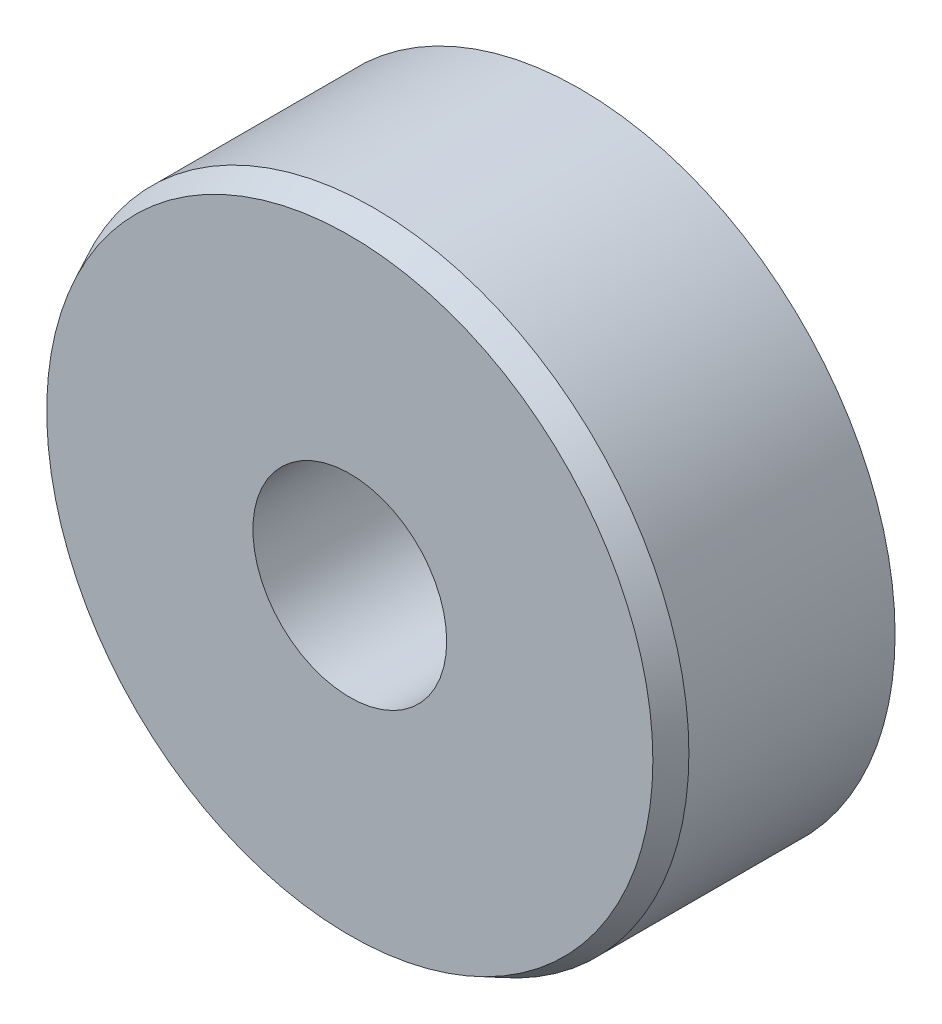
SolidWorks part; units mm, degrees
ref_plane "Front" through (0, 0, 0) normal (0, 0, 1) x (1, 0, 0)
ref_plane "Top" through (0, 0, 0) normal (0, 1, 0) x (1, 0, 0)
ref_plane "Right" through (0, 0, 0) normal (1, 0, 0) x (0, 0, -1)
sketch "Sketch1" plane through (0, 0, 0) normal (0, 0, 1) x (1, 0, 0)
  circle A0 centre (0, 0) radius 2
  circle A1 centre (0, 0) radius 6.5
  dimension "D1" = 4
  dimension "D2" = 13
extrude "Boss-Extrude1" add sketch "Sketch1" along normal blind 5
chamfer "Chamfer1" distance 0.5 angle 26 2 edges at (6.5, 0, 0) (6.5, 0, 5)
